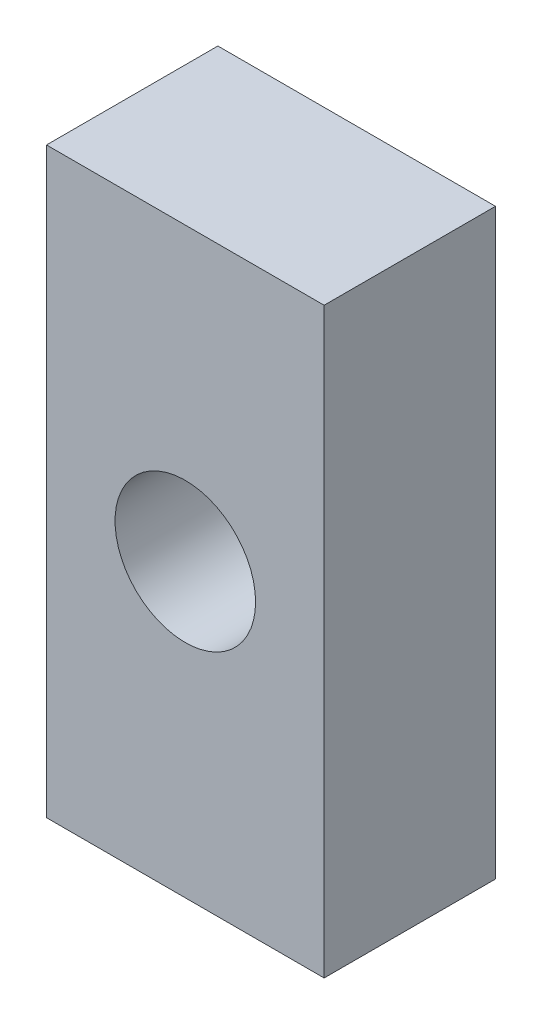
SolidWorks part; units mm, degrees
ref_plane "Front Plane" through (0, 0, 0) normal (0, 0, 1) x (1, 0, 0)
ref_plane "Top Plane" through (0, 0, 0) normal (0, 1, 0) x (1, 0, 0)
ref_plane "Right Plane" through (0, 0, 0) normal (1, 0, 0) x (0, 0, -1)
sketch "Sketch1" plane through (0, 0, 0) normal (0, 0, 1) x (1, 0, 0)
  line L0 (-14.45, 0) -> (14.45, 0) construction
  line L1 (-18.5, -8.5) -> (18.5, -8.5) construction
  line L2 (-18.5, -8.5) -> (-18.5, 8.5) construction
  line L3 (-18.5, 8.5) -> (18.5, 8.5) construction
  line L4 (18.5, -8.5) -> (18.5, 8.5) construction
  line L5 (-18.5, -8.5) -> (18.5, 8.5) construction
  line L6 (-18.5, 8.5) -> (18.5, -8.5) construction
  line L7 (-12.4, 4.7773) -> (12.4, 4.7773) construction
  line L9 (-10.4, -8.5) -> (-18.5, -8.5)
  line L10 (-10.4, -8.5) -> (-10.4, 8.5)
  line L11 (-10.4, 8.5) -> (-18.5, 8.5)
  line L12 (-18.5, -8.5) -> (-18.5, 8.5)
  line L13 (-10.4, -8.5) -> (-18.5, 8.5) construction
  line L14 (-10.4, 8.5) -> (-18.5, -8.5) construction
  circle A0 centre (-14.45, 0) radius 2.05
  circle A1 centre (14.45, 0) radius 2.05 construction
  point P0 (0, 0)
  point P10 (-12.4, 0)
  point P12 (12.4, 0)
  point P14 (-16.5, 0)
  dimension "D4" = 4.1
  dimension "D1" = 17
  dimension "D2" = 2
  dimension "D5" = 24.8
extrude "Boss-Extrude1" add sketch "Sketch1" along normal blind 5
